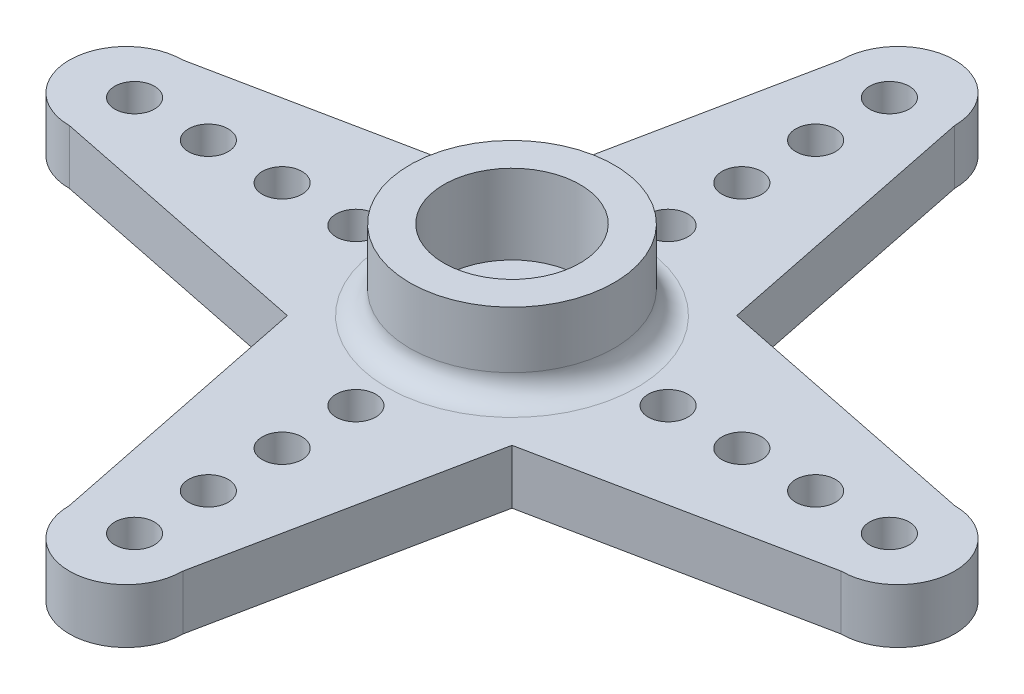
SolidWorks part; units mm, degrees
ref_plane "Front Plane" through (0, 0, 0) normal (0, 0, 1) x (1, 0, 0)
ref_plane "Top Plane" through (0, 0, 0) normal (0, 1, 0) x (1, 0, 0)
ref_plane "Right Plane" through (0, 0, 0) normal (1, 0, 0) x (0, 0, -1)
sketch "Sketch1" plane through (0, 0, 0) normal (0, 1, 0) x (1, 0, 0)
  line L0 (0, 0) -> (4.9497, 4.9497) construction
  line L1 (0, 0) -> (4.9497, -4.9497) construction
  line L2 (0, 0) -> (-4.9497, -4.9497) construction
  line L3 (0, 0) -> (-4.9497, 4.9497) construction
  line L4 (0, 1.5) -> (0, 19.5) construction
  line L5 (1.5, 0) -> (19.5, 0) construction
  line L6 (0, -1.5) -> (0, -19.5) construction
  line L7 (-1.5, 0) -> (-19.5, 0) construction
  line L8 (-16.9992, 2.5) -> (-4.9497, 4.9497)
  line L9 (-16.9992, -2.5) -> (-4.9497, -4.9497)
  line L10 (-4.9497, -4.9497) -> (-2.5, -17)
  line L11 (2.5, -17) -> (4.9497, -4.9497)
  line L12 (4.9497, -4.9497) -> (17.0009, -2.5)
  line L13 (17.0009, 2.5) -> (4.9497, 4.9497)
  line L14 (4.9497, 4.9497) -> (2.5, 17.0016)
  line L15 (-2.5, 17.0016) -> (-4.9497, 4.9497)
  circle A0 centre (0, 0) radius 1.5
  arc A1 (-16.9992, 2.5) -> (-16.9992, -2.5) centre (-16.9992, 0) ccw
  arc A2 (17.0009, -2.5) -> (17.0009, 2.5) centre (17.0009, 0) ccw
  arc A3 (2.5, 17.0016) -> (-2.5, 17.0016) centre (0, 17.0016) ccw
  arc A4 (-2.5, -17) -> (2.5, -17) centre (0, -17) ccw
  dimension "D1" = 3
  dimension "D10" = 5
  dimension "D11" = 5
  dimension "D12" = 5
  dimension "D13" = 5
  dimension "D2" = 7
  dimension "D3" = 7
  dimension "D4" = 7
  dimension "D5" = 7
  dimension "D6" = 18
  dimension "D7" = 18
  dimension "D8" = 18
  dimension "D9" = 18
extrude "Boss-Extrude1" add sketch "Sketch1" along normal blind 2.4
sketch "Sketch2" plane through (0, 2.4, 0) normal (0, 1, 0) x (1, 0, 0)
  circle A0 centre (0, 0) radius 4.5
  circle A1 centre (0, 0) radius 3
  dimension "D1" = 9
  dimension "D2" = 1.5
extrude "Boss-Extrude2" add sketch "Sketch2" along normal blind 3.5
fillet "Fillet1" radius 1 1 edges at (0, 2.4, 4.5)
sketch "Sketch3" plane through (0, 2.4, 0) normal (0, 1, 0) x (1, 0, 0)
  line L0 (0, 0) -> (0, 19.5016) construction
  line L1 (0, 17.5016) -> (0, 19.5016)
  line L2 (0, 15.7516) -> (0, 14.2516)
  line L3 (0, 11.0016) -> (0, 12.5016)
  line L4 (0, 7.7516) -> (0, 9.2516)
  line L5 (0, 7.7516) -> (0, 19.5016)
  line L6 (0, 0) -> (22.1255, 22.1255) construction
  line L7 (0, 0) -> (-17.5016, 17.5016) construction
  line L8 (0, 0) -> (18.7166, -18.7166) construction
  line L9 (0, 0) -> (19.5009, 0) construction
  arc A0 (2.5, 17.0016) -> (-2.5, 17.0016) centre (0, 17.0016) ccw construction
  circle A1 centre (0, 16.6266) radius 0.875
  circle A2 centre (0, 13.3766) radius 0.875
  circle A3 centre (0, 10.1266) radius 0.875
  circle A4 centre (0, 6.8766) radius 0.875
  circle A5 centre (6.8766, 0) radius 0.875
  circle A6 centre (10.1266, 0) radius 0.875
  circle A7 centre (13.3766, 0) radius 0.875
  circle A8 centre (16.6266, 0) radius 0.875
  circle A9 centre (0, -16.6266) radius 0.875
  circle A10 centre (0, -13.3766) radius 0.875
  circle A11 centre (0, -10.1266) radius 0.875
  circle A12 centre (0, -6.8766) radius 0.875
  circle A13 centre (-16.6266, 0) radius 0.875
  circle A14 centre (-13.3766, 0) radius 0.875
  circle A15 centre (-10.1266, 0) radius 0.875
  circle A16 centre (-6.8766, 0) radius 0.875
  arc A17 (17.0009, -2.5) -> (17.0009, 2.5) centre (17.0009, 0) ccw construction
  dimension "D1" = 1.75
  dimension "D2" = 1.75
  dimension "D3" = 1.75
  dimension "D4" = 1.75
  dimension "D5" = 2
  dimension "D6" = 1.5
  dimension "D7" = 1.5
  dimension "D8" = 1.5
  dimension "D9" = 16.6266
  dimension "D10" = 19.5009
extrude "Cut-Extrude1" cut sketch "Sketch3" against normal blind 3.5 contours A9 | A10 | A11 | A12 | A16 | A15 | A14 | A13 | A4 | L5 A3 | L5 A3 | L5 A2 | L5 A2 | L5 A1 | L5 A1 | A5 | A7 | A8 | A6
sketch "Sketch4" plane through (0, 0, 0) normal (0, -1, 0) x (1, 0, 0)
  circle A0 centre (0, 0) radius 4.375
  dimension "D1" = 8.75
extrude "Cut-Extrude2" cut sketch "Sketch4" against normal blind 0.5
